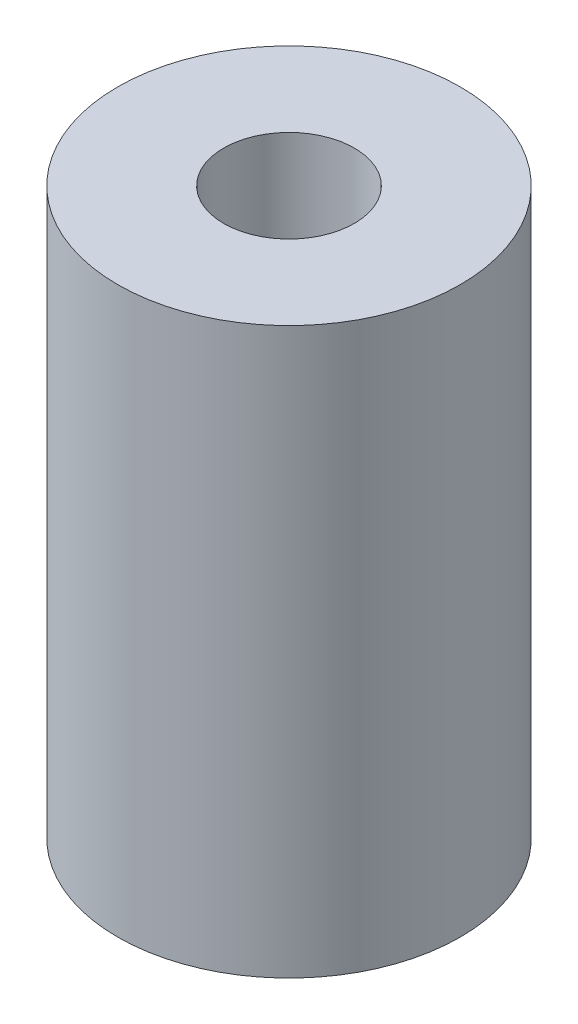
SolidWorks part; units mm, degrees
ref_plane "前视基准面" through (0, 0, 0) normal (0, 0, 1) x (1, 0, 0)
ref_plane "上视基准面" through (0, 0, 0) normal (0, 1, 0) x (1, 0, 0)
ref_plane "右视基准面" through (0, 0, 0) normal (1, 0, 0) x (0, 0, -1)
other "Configuration Table"
sketch "草图1" plane through (0, 0, 0) normal (0, 1, 0) x (1, 0, 0)
  circle A0 centre (0, 0) radius 1.85
  dimension "D1" = 3.7
extrude "拉伸-薄壁1" add sketch "草图1" along normal blind 16 thin
